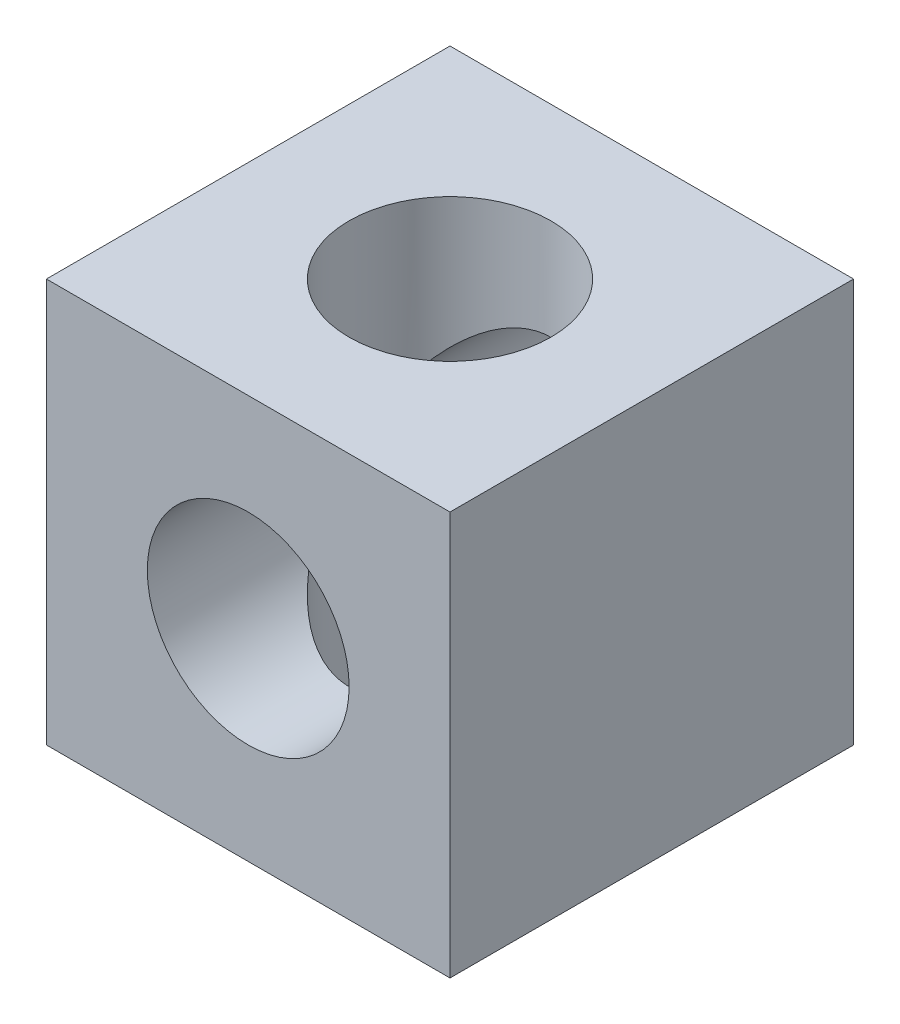
SolidWorks part; units mm, degrees
ref_plane "Front Plane" through (0, 0, 0) normal (0, 0, 1) x (1, 0, 0)
ref_plane "Top Plane" through (0, 0, 0) normal (0, 1, 0) x (1, 0, 0)
ref_plane "Right Plane" through (0, 0, 0) normal (1, 0, 0) x (0, 0, -1)
sketch "Sketch1" plane through (0, 0, 0) normal (0, 1, 0) x (1, 0, 0)
  line L1 (0, 0) -> (19, 0)
  line L2 (0, 0) -> (0, 19)
  line L3 (0, 19) -> (19, 19)
  line L4 (19, 0) -> (19, 19)
  dimension "D1" = 19
  dimension "D2" = 19
extrude "Boss-Extrude1" add sketch "Sketch1" along normal blind 19
sketch "Sketch2" plane through (0, 19, 0) normal (0, 1, 0) x (1, 0, 0)
  line L0 (0, 19) -> (0, 0) construction
  line L1 (0, 0) -> (19, 0) construction
  circle A0 centre (9.5, 9.5) radius 4.75
  dimension "D1" = 9.5
  dimension "D2" = 9.5
  dimension "D3" = 9.5
extrude "Cut-Extrude1" cut sketch "Sketch2" against normal up to surface (19 mm away) up to face at (9.5, 0, -9.5)
sketch "Sketch3" plane through (0, 0, 0) normal (0, 0, 1) x (1, 0, 0)
  line L0 (0, 19) -> (0, 0) construction
  line L1 (0, 0) -> (19, 0) construction
  circle A0 centre (9.5, 9.5) radius 4.75
  dimension "D1" = 9.5
  dimension "D2" = 9.5
  dimension "D3" = 9.5
extrude "Cut-Extrude2" cut sketch "Sketch3" against normal blind 19
